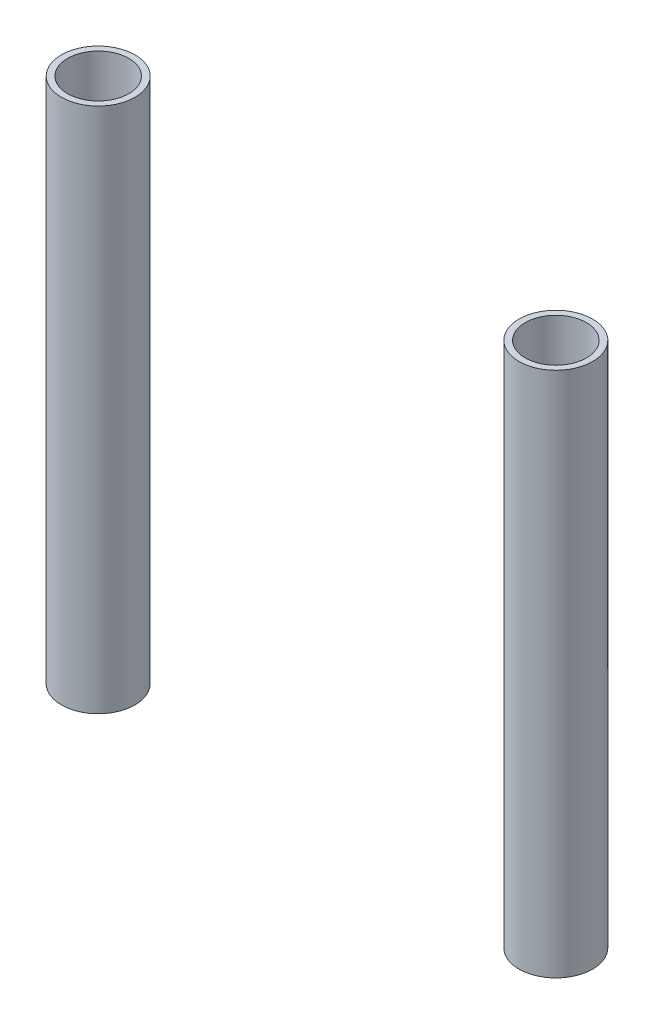
SolidWorks part; units mm, degrees
ref_plane "Front" through (0, 0, 0) normal (0, 0, 1) x (1, 0, 0)
ref_plane "Top" through (0, 0, 0) normal (0, 1, 0) x (1, 0, 0)
ref_plane "Right" through (0, 0, 0) normal (1, 0, 0) x (0, 0, -1)
sketch "Sketch1" plane through (0, 0, 0) normal (0, 1, 0) x (1, 0, 0)
  line L0 (50, 0) -> (-50, 0) construction
  line L1 (0, 0) -> (0, 6.5479) construction
  circle A0 centre (-50, 0) radius 8.039
  circle A1 centre (50, 0) radius 6.6928
  circle A2 centre (-50, 0) radius 6.6928
  circle A3 centre (50, 0) radius 8.039
  point P4 (0, 0)
  dimension "D1" = 100
  dimension "D2" = 16.078
  dimension "D3" = 1.3462
extrude "Boss-Extrude1" add sketch "Sketch1" along normal blind 115
